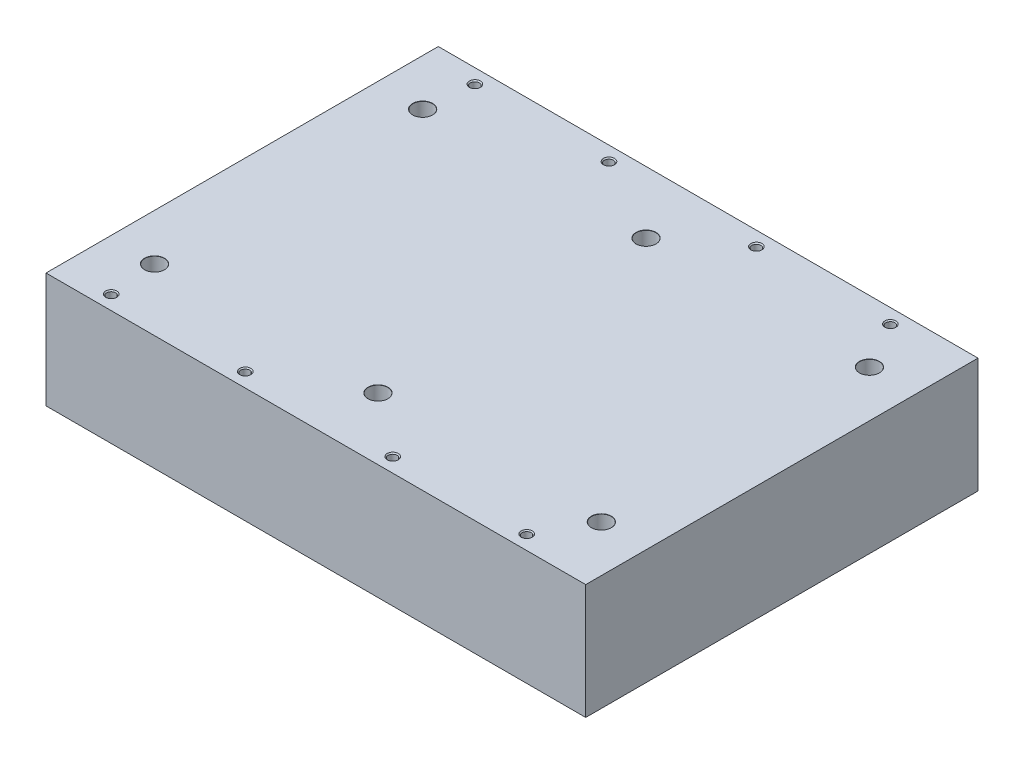
SolidWorks part; units mm, degrees
material "6061-T6 (SS)"
ref_plane "Front Plane" through (0, 0, 0) normal (0, 0, 1) x (1, 0, 0)
ref_plane "Top Plane" through (0, 0, 0) normal (0, 1, 0) x (1, 0, 0)
ref_plane "Right Plane" through (0, 0, 0) normal (1, 0, 0) x (0, 0, -1)
sketch "Sketch1" plane through (0, 0, 0) normal (0, 1, 0) x (1, 0, 0)
  line L1 (0, 0) -> (302, 0)
  line L2 (0, 0) -> (0, 219.5)
  line L3 (0, 219.5) -> (302, 219.5)
  line L4 (302, 0) -> (302, 219.5)
  dimension "D1" = 302
  dimension "D2" = 219.5
extrude "Boss-Extrude1" add sketch "Sketch1" along normal blind 64.4
hole_wizard "M6x1.0 Tapped Hole1" positions "Sketch2" profile "Sketch3" tap size "M6x1.0" standard "ANSI Metric"
sketch "Sketch2" plane through (0, 64.4, 0) normal (0, 1, 0) x (1, 0, 0)
  line L0 (0, 0) -> (302, 0) construction
  line L1 (0, 219.5) -> (0, 0) construction
  point P0 (28.5, 8)
  point P2 (103.5, 8)
  point P4 (186, 8)
  point P6 (261, 8)
  point P8 (261, 211.5)
  point P10 (186, 211.5)
  point P12 (103.5, 211.5)
  point P14 (28.5, 211.5)
  dimension "D1" = 8
  dimension "D2" = 211.5
  dimension "D3" = 28.5
  dimension "D4" = 75
  dimension "D5" = 82.5
  dimension "D6" = 75
sketch "Sketch3" plane through (28.5, 64.4, -8) normal (1, 0, 0) x (0, 0, 1)
  line L0 (0, 0) -> (0, 17.5022)
  line L1 (0, 17.5022) -> (2.5, 16)
  line L2 (2.5, 16) -> (2.5, 0.6)
  line L3 (2.5, 0.6) -> (3.1, 0)
  line L5 (3.1, 0) -> (0, 0)
  line L6 (-2.5, 0.6) -> (-3.1, 0) construction
  line L10 (0, 17.5022) -> (-2.5, 16) construction
  line L11 (0, -6.35) -> (0, 107.95) construction
  dimension "Tap Drill Dia." = 5
  dimension "Tap Drill Depth" = 16
  dimension "Near C'Sink Dia." = 6.2
  dimension "Near C'Sink Angle" = 90
  dimension "Drill Angle" = 118
cosmetic thread "Hole Thread1" parameters "D1"=12, "D2"=6
cosmetic thread "Hole Thread2" parameters "D1"=12, "D2"=6
cosmetic thread "Hole Thread3" parameters "D1"=12, "D2"=6
cosmetic thread "Hole Thread4" parameters "D1"=12, "D2"=6
cosmetic thread "Hole Thread5" parameters "D1"=12, "D2"=6
cosmetic thread "Hole Thread6" parameters "D1"=12, "D2"=6
cosmetic thread "Hole Thread7" parameters "D1"=12, "D2"=6
cosmetic thread "Hole Thread8" parameters "D1"=12, "D2"=6
hole_wizard "CBORE for M6 SHCS1" positions "Sketch4" profile "Sketch5" counterbore size "M6" standard "ANSI Metric" end condition through all
sketch "Sketch4" plane through (0, 64.4, 0) normal (0, 1, 0) x (1, 0, 0)
  line L0 (0, 219.5) -> (0, 0) construction
  line L1 (0, 0) -> (302, 0) construction
  point P0 (26, 34.75)
  point P2 (26, 184.75)
  point P4 (151, 184.75)
  point P6 (151, 34.75)
  point P8 (276, 34.75)
  point P10 (276, 184.75)
  dimension "D1" = 26
  dimension "D2" = 150
  dimension "D3" = 34.75
  dimension "D4" = 125
  dimension "D5" = 125
sketch "Sketch5" plane through (26, 64.4, -34.75) normal (1, 0, 0) x (0, 0, 1)
  line L0 (0, 0) -> (0, 64.4)
  line L1 (0, 64.4) -> (3.2, 64.4)
  line L3 (3.2, 64.4) -> (3.2, 20)
  line L4 (5.5, 20) -> (3.2, 20)
  line L5 (5.5, 20) -> (5.5, 0.1)
  line L6 (5.5, 0.1) -> (5.6, 0)
  line L7 (5.6, 0) -> (0, 0)
  line L8 (-5.5, 0.1) -> (-5.6, 0) construction
  line L11 (0, -6.35) -> (0, 107.95) construction
  dimension "Thru Hole Dia." = 6.4
  dimension "Thru Hole Depth" = 64.4
  dimension "C'Bore Dia." = 11
  dimension "C'Bore Depth" = 20
  dimension "Near C'Sink Dia." = 11.2
  dimension "Near C'Sink Angle" = 90
